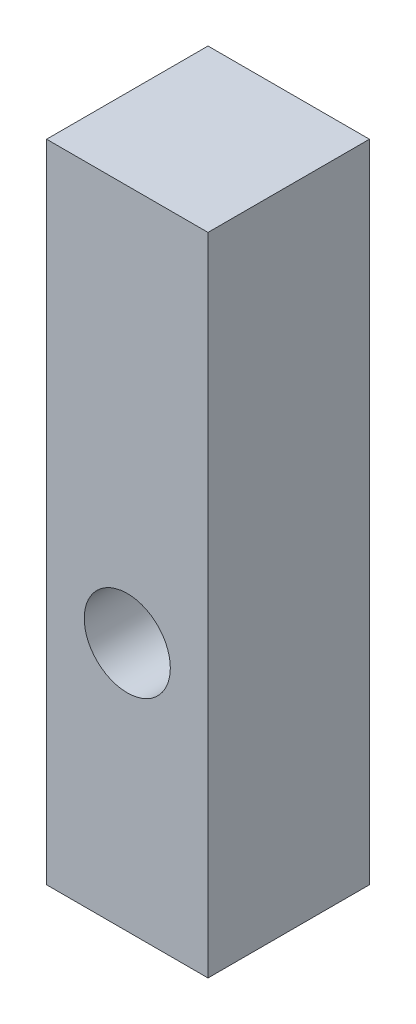
SolidWorks part; units mm, degrees
ref_plane "Спереди" through (0, 0, 0) normal (0, 0, 1) x (1, 0, 0)
ref_plane "Сверху" through (0, 0, 0) normal (0, 1, 0) x (1, 0, 0)
ref_plane "Справа" through (0, 0, 0) normal (1, 0, 0) x (0, 0, -1)
sketch "Sketch1" plane through (0, 0, 0) normal (0, 1, 0) x (1, 0, 0)
  line L1 (7.5, -7.5) -> (-7.5, -7.5)
  line L2 (7.5, -7.5) -> (7.5, 7.5)
  line L3 (7.5, 7.5) -> (-7.5, 7.5)
  line L4 (-7.5, -7.5) -> (-7.5, 7.5)
  line L5 (7.5, -7.5) -> (-7.5, 7.5) construction
  line L6 (7.5, 7.5) -> (-7.5, -7.5) construction
  point P0 (0, 0)
  dimension "D1" = 15
extrude "Boss-Extrude1" add sketch "Sketch1" along normal blind 60
sketch "Sketch2" plane through (0, 0, 7.5) normal (0, 0, 1) x (1, 0, 0)
  line L0 (-7.5, 23.1963) -> (7.5, 23.1963) construction
  line L1 (-7.5, 60) -> (-7.5, 0) construction
  line L2 (7.5, 60) -> (7.5, 0) construction
  circle A0 centre (0, 23.1963) radius 4
  dimension "D1" = 8
extrude "Cut-Extrude1" cut sketch "Sketch2" against normal through all
